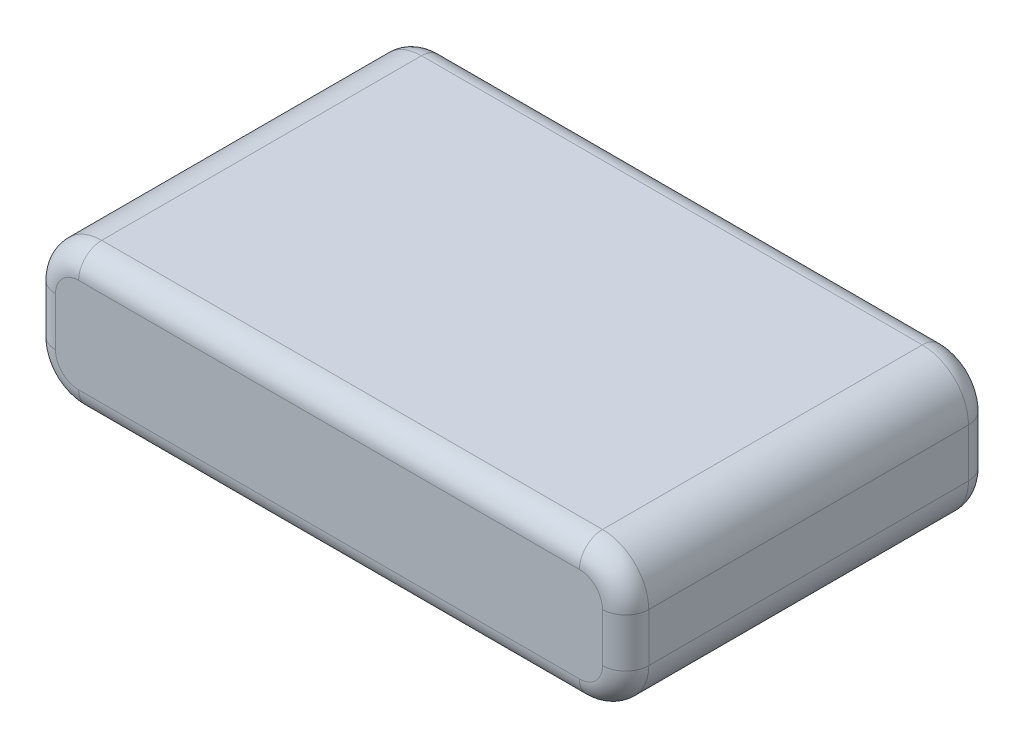
SolidWorks part; units mm, degrees
ref_plane "Front Plane" through (0, 0, 0) normal (0, 0, 1) x (1, 0, 0)
ref_plane "Top Plane" through (0, 0, 0) normal (0, 1, 0) x (1, 0, 0)
ref_plane "Right Plane" through (0, 0, 0) normal (1, 0, 0) x (0, 0, -1)
sketch "Sketch1" plane through (0, 0, 0) normal (0, 1, 0) x (1, 0, 0)
  line L1 (-19.25, 11.875) -> (19.25, 11.875)
  line L2 (-19.25, 11.875) -> (-19.25, -11.875)
  line L3 (-19.25, -11.875) -> (19.25, -11.875)
  line L4 (19.25, 11.875) -> (19.25, -11.875)
  line L5 (-19.25, 11.875) -> (19.25, -11.875) construction
  line L6 (-19.25, -11.875) -> (19.25, 11.875) construction
  point P0 (0, 0)
  dimension "D1" = 23.75
  dimension "D2" = 38.5
extrude "Boss-Extrude1" add sketch "Sketch1" along normal blind 9.15
fillet "Fillet1" radius 3 4 edges at (-19.25, 0, 0) (-19.25, 9.15, 0) (19.25, 0, 0) (19.25, 9.15, 0)
fillet "Fillet2" radius 1.5 16 edges at (18.3713, 0.8787, -11.875) (19.25, 4.575, -11.875) (18.3713, 8.2713, -11.875) (0, 9.15, -11.875) (-18.3713, 8.2713, -11.875) (-19.25, 4.575, -11.875) (-18.3713, 0.8787, -11.875) (0, 0, -11.875) (-18.3713, 8.2713, 11.875) (0, 9.15, 11.875) (18.3713, 8.2713, 11.875) (19.25, 4.575, 11.875) (18.3713, 0.8787, 11.875) (0, 0, 11.875) (-18.3713, 0.8787, 11.875) (-19.25, 4.575, 11.875)
